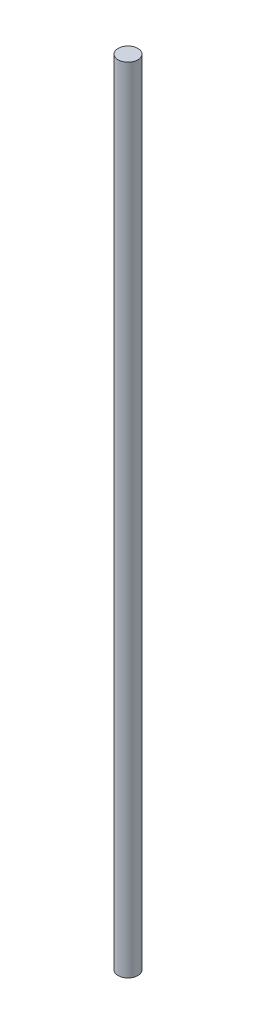
SolidWorks part; units mm, degrees
ref_plane "Front Plane" through (0, 0, 0) normal (0, 0, 1) x (1, 0, 0)
ref_plane "Top Plane" through (0, 0, 0) normal (0, 1, 0) x (1, 0, 0)
ref_plane "Right Plane" through (0, 0, 0) normal (1, 0, 0) x (0, 0, -1)
sketch "Sketch1" plane through (0, 0, 0) normal (0, 1, 0) x (1, 0, 0)
  circle A0 centre (0, 0) radius 3.175
  dimension "D1" = 6.35
extrude "Boss-Extrude1" add sketch "Sketch1" along normal blind 254
